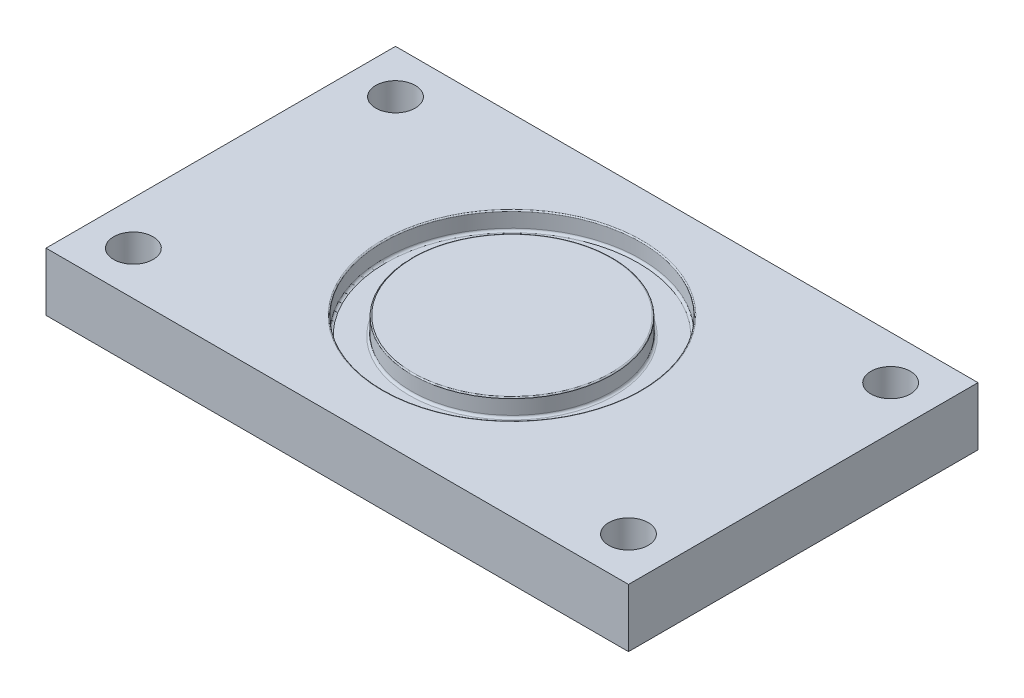
SolidWorks part; units mm, degrees
material "Al 6061-T6"
ref_plane "Front Plane" through (0, 0, 0) normal (0, 0, 1) x (1, 0, 0)
ref_plane "Top Plane" through (0, 0, 0) normal (0, 1, 0) x (1, 0, 0)
ref_plane "Right Plane" through (0, 0, 0) normal (1, 0, 0) x (0, 0, -1)
sketch "Sketch1" plane through (0, 0, 0) normal (0, 1, 0) x (1, 0, 0)
  line L1 (31.75, -19.05) -> (-31.75, -19.05)
  line L2 (31.75, -19.05) -> (31.75, 19.05)
  line L3 (31.75, 19.05) -> (-31.75, 19.05)
  line L4 (-31.75, -19.05) -> (-31.75, 19.05)
  line L5 (31.75, -19.05) -> (-31.75, 19.05) construction
  line L6 (31.75, 19.05) -> (-31.75, -19.05) construction
  point P0 (0, 0)
  dimension "D1" = 63.5
  dimension "D2" = 38.1
extrude "Boss-Extrude1" add sketch "Sketch1" along normal blind 6.35
sketch "Sketch2" plane through (0, 6.35, 0) normal (0, 1, 0) x (1, 0, 0)
  circle A0 centre (0, 0) radius 10.9474
  circle A1 centre (0, 0) radius 14.0462
  dimension "D1" = 21.8948
  dimension "D2" = 3.0988
extrude "Cut-Extrude1" cut sketch "Sketch2" against normal blind 1.9558
hole_wizard "#8 Clearance Hole1" positions "Sketch3" profile "Sketch4" hole size "#8" standard "ANSI Inch" end condition through all
sketch "Sketch3" plane through (0, 0, 0) normal (0, -1, 0) x (-1, 0, 0)
  line L0 (31.75, 19.05) -> (31.75, -19.05) construction
  line L1 (31.75, -19.05) -> (-31.75, -19.05) construction
  point P0 (26.9875, -14.2875)
  point P12 (-26.9875, -14.2875)
  point P13 (-26.9875, 14.2875)
  point P14 (26.9875, 14.2875)
  dimension "D1" = 4.7625
  dimension "D2" = 4.7625
  dimension "D3" = 2
  dimension "D4" = 2
sketch "Sketch4" plane through (-26.9875, 0, 14.2875) normal (1, 0, 0) x (0, 0, -1)
  line L0 (0, 0) -> (0, 6.35)
  line L1 (0, 6.35) -> (2.1526, 6.35)
  line L2 (2.1526, 6.35) -> (2.1526, 0)
  line L5 (2.1526, 0) -> (0, 0)
  line L11 (0, -6.35) -> (0, 107.95) construction
  dimension "Thru Hole Dia." = 4.3053
  dimension "Thru Hole Depth" = 6.35
fillet "Fillet1" radius 0.127 2 edges at (0, 6.35, 10.9474) (0, 6.35, 14.0462)
fillet "Fillet2" radius 0.254 2 edges at (0, 4.3942, 10.9474) (0, 4.3942, 14.0462)
